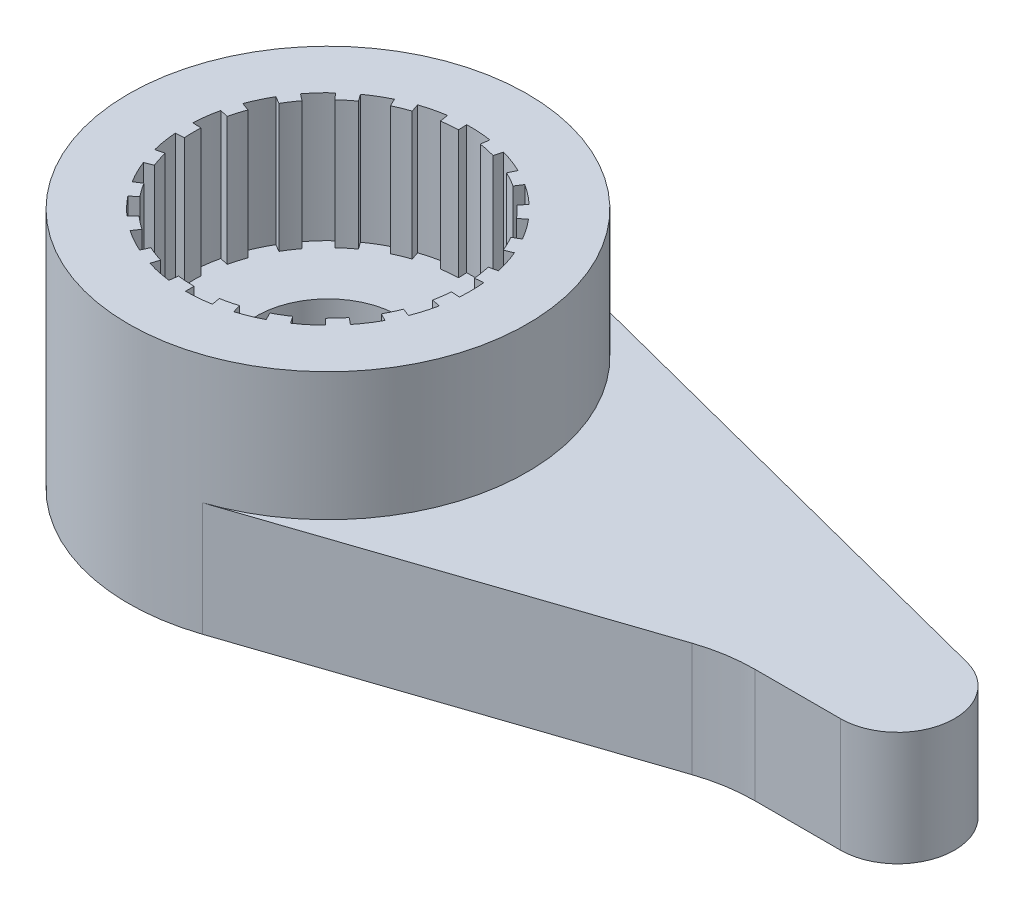
SolidWorks part; units mm, degrees
material "Nylon 6/10"
ref_plane "Front plane" through (0, 0, 0) normal (0, 0, 1) x (1, 0, 0)
ref_plane "Top plane" through (0, 0, 0) normal (0, 1, 0) x (1, 0, 0)
ref_plane "Right Plane" through (0, 0, 0) normal (1, 0, 0) x (0, 0, -1)
sketch "Sketch1" plane through (0, 0, 0) normal (0, 1, 0) x (1, 0, 0)
  circle A0 centre (0, 0) radius 2.5
  circle A1 centre (0, 0) radius 3.5
  dimension "D1" = 5
  dimension "D2" = 7
extrude "Boss-Extrude1" add sketch "Sketch1" along normal blind 2.25
sketch "Sketch6" plane through (0, 0, 0) normal (0, -1, 0) x (1, 0, 0)
  line L0 (0.4341, 2.462) -> (0.4081, 2.3143)
  line L1 (0.6927, 2.2456) -> (0.7369, 2.3889)
  line L2 (0, 2.35) -> (0, 0) construction
  line L3 (0, 0) -> (0.6927, 2.2456) construction
  line L4 (0, 0) -> (0.4081, 2.3143) construction
  line L5 (1.1405, 2.2247) -> (1.0721, 2.0912)
  line L6 (1.3238, 1.9417) -> (1.4083, 2.0656)
  line L7 (1.7456, 1.7897) -> (1.6409, 1.6823)
  line L8 (1.8373, 1.4652) -> (1.9546, 1.5587)
  line L9 (2.1956, 1.1956) -> (2.0638, 1.1239)
  line L10 (2.1876, 0.8586) -> (2.3272, 0.9134)
  line L11 (2.4504, 0.4954) -> (2.3034, 0.4656)
  line L12 (2.3434, 0.1756) -> (2.493, 0.1868)
  line L13 (2.4876, -0.2489) -> (2.3383, -0.234)
  line L14 (2.2911, -0.5229) -> (2.4373, -0.5563)
  line L15 (2.3037, -0.9711) -> (2.1655, -0.9128)
  line L16 (2.0352, -1.175) -> (2.1651, -1.25)
  line L17 (1.9151, -1.607) -> (1.8002, -1.5106)
  line L18 (1.5984, -1.7227) -> (1.7004, -1.8326)
  line L19 (1.3564, -2.1001) -> (1.275, -1.9741)
  line L20 (1.0196, -2.1173) -> (1.0847, -2.2524)
  line L21 (0.6771, -2.4066) -> (0.6365, -2.2622)
  line L22 (0.3502, -2.3238) -> (0.3726, -2.4721)
  line L23 (-0.0623, -2.4992) -> (-0.0586, -2.3493)
  line L24 (-0.3502, -2.3238) -> (-0.3726, -2.4721)
  line L25 (-0.7962, -2.3698) -> (-0.7484, -2.2276)
  line L26 (-1.0196, -2.1173) -> (-1.0847, -2.2524)
  line L27 (-1.4594, -2.0298) -> (-1.3718, -1.9081)
  line L28 (-1.5984, -1.7227) -> (-1.7004, -1.8326)
  line L29 (-1.9928, -1.5095) -> (-1.8733, -1.4189)
  line L30 (-2.0352, -1.175) -> (-2.1651, -1.25)
  line L31 (-2.3492, -0.8551) -> (-2.2083, -0.8037)
  line L32 (-2.2911, -0.5229) -> (-2.4373, -0.5563)
  line L33 (-2.4969, -0.1246) -> (-2.3471, -0.1171)
  line L34 (-2.3434, 0.1756) -> (-2.493, 0.1868)
  line L35 (-2.4227, 0.6169) -> (-2.2773, 0.5799)
  line L36 (-2.1876, 0.8586) -> (-2.3272, 0.9134)
  line L37 (-2.1332, 1.3036) -> (-2.0052, 1.2254)
  line L38 (-1.8373, 1.4652) -> (-1.9546, 1.5587)
  line L39 (-1.6542, 1.8745) -> (-1.555, 1.762)
  line L40 (-1.3238, 1.9417) -> (-1.4083, 2.0656)
  line L41 (-1.0282, 2.2788) -> (-0.9665, 2.142)
  line L42 (-0.6927, 2.2456) -> (-0.7369, 2.3889)
  line L43 (-0.3109, 2.4806) -> (-0.2922, 2.3318)
  line L44 (0, 2.35) -> (0, 2.5)
  arc A0 (0.6927, 2.2456) -> (0.4081, 2.3143) centre (0, 0) ccw
  circle A1 centre (0, 0) radius 2.5 construction
  arc A3 (0.7369, 2.3889) -> (0.4341, 2.462) centre (0, 0) ccw
  arc A4 (0.4081, 2.3143) -> (0, 2.35) centre (0, 0) ccw construction
  arc A5 (1.4083, 2.0656) -> (1.1405, 2.2247) centre (0, 0) ccw
  arc A6 (1.3238, 1.9417) -> (1.0721, 2.0912) centre (0, 0) ccw
  arc A7 (1.9546, 1.5587) -> (1.7456, 1.7897) centre (0, 0) ccw
  arc A8 (1.8373, 1.4652) -> (1.6409, 1.6823) centre (0, 0) ccw
  arc A9 (2.3272, 0.9134) -> (2.1956, 1.1956) centre (0, 0) ccw
  arc A10 (2.1876, 0.8586) -> (2.0638, 1.1239) centre (0, 0) ccw
  arc A11 (2.493, 0.1868) -> (2.4504, 0.4954) centre (0, 0) ccw
  arc A12 (2.3434, 0.1756) -> (2.3034, 0.4656) centre (0, 0) ccw
  arc A13 (2.4373, -0.5563) -> (2.4876, -0.2489) centre (0, 0) ccw
  arc A14 (2.2911, -0.5229) -> (2.3383, -0.234) centre (0, 0) ccw
  arc A15 (2.1651, -1.25) -> (2.3037, -0.9711) centre (0, 0) ccw
  arc A16 (2.0352, -1.175) -> (2.1655, -0.9128) centre (0, 0) ccw
  arc A17 (1.7004, -1.8326) -> (1.9151, -1.607) centre (0, 0) ccw
  arc A18 (1.5984, -1.7227) -> (1.8002, -1.5106) centre (0, 0) ccw
  arc A19 (1.0847, -2.2524) -> (1.3564, -2.1001) centre (0, 0) ccw
  arc A20 (1.0196, -2.1173) -> (1.275, -1.9741) centre (0, 0) ccw
  arc A21 (0.3726, -2.4721) -> (0.6771, -2.4066) centre (0, 0) ccw
  arc A22 (0.3502, -2.3238) -> (0.6365, -2.2622) centre (0, 0) ccw
  arc A23 (-0.3726, -2.4721) -> (-0.0623, -2.4992) centre (0, 0) ccw
  arc A24 (-0.3502, -2.3238) -> (-0.0586, -2.3493) centre (0, 0) ccw
  arc A25 (-1.0847, -2.2524) -> (-0.7962, -2.3698) centre (0, 0) ccw
  arc A26 (-1.0196, -2.1173) -> (-0.7484, -2.2276) centre (0, 0) ccw
  arc A27 (-1.7004, -1.8326) -> (-1.4594, -2.0298) centre (0, 0) ccw
  arc A28 (-1.5984, -1.7227) -> (-1.3718, -1.9081) centre (0, 0) ccw
  arc A29 (-2.1651, -1.25) -> (-1.9928, -1.5095) centre (0, 0) ccw
  arc A30 (-2.0352, -1.175) -> (-1.8733, -1.4189) centre (0, 0) ccw
  arc A31 (-2.4373, -0.5563) -> (-2.3492, -0.8551) centre (0, 0) ccw
  arc A32 (-2.2911, -0.5229) -> (-2.2083, -0.8037) centre (0, 0) ccw
  arc A33 (-2.493, 0.1868) -> (-2.4969, -0.1246) centre (0, 0) ccw
  arc A34 (-2.3434, 0.1756) -> (-2.3471, -0.1171) centre (0, 0) ccw
  arc A35 (-2.3272, 0.9134) -> (-2.4227, 0.6169) centre (0, 0) ccw
  arc A36 (-2.1876, 0.8586) -> (-2.2773, 0.5799) centre (0, 0) ccw
  arc A37 (-1.9546, 1.5587) -> (-2.1332, 1.3036) centre (0, 0) ccw
  arc A38 (-1.8373, 1.4652) -> (-2.0052, 1.2254) centre (0, 0) ccw
  arc A39 (-1.4083, 2.0656) -> (-1.6542, 1.8745) centre (0, 0) ccw
  arc A40 (-1.3238, 1.9417) -> (-1.555, 1.762) centre (0, 0) ccw
  arc A41 (-0.7369, 2.3889) -> (-1.0282, 2.2788) centre (0, 0) ccw
  arc A42 (-0.6927, 2.2456) -> (-0.9665, 2.142) centre (0, 0) ccw
  arc A43 (0, 2.5) -> (-0.3109, 2.4806) centre (0, 0) ccw
  arc A44 (0, 2.35) -> (-0.2922, 2.3318) centre (0, 0) ccw
  dimension "D1" = 0.15
  dimension "D2" = 17.143
  dimension "D3" = 10
  dimension "D4" = 21
extrude "Boss-Extrude4" add sketch "Sketch6" against normal up to surface (2.25 mm away) up to face at (0, 2.25, 3.5)
sketch "Sketch2" plane through (0, 0, 0) normal (0, 1, 0) x (1, 0, 0)
  line L0 (10.25, 0.9682) -> (0.875, 3.3889)
  line L2 (0, 0) -> (10, 0) construction
  line L6 (1.1153, -3.3176) -> (7.5441, -1.1564)
  line L7 (8.5, -1) -> (10, -1)
  circle A0 centre (0, 0) radius 3.5 construction
  arc A1 (1.1153, -3.3176) -> (0.875, 3.3889) centre (0, 0) ccw
  arc A2 (10, -1) -> (10.25, 0.9682) centre (10, 0) ccw
  arc A5 (7.5441, -1.1564) -> (8.5, -1) centre (8.5, -4) cw
  dimension "D1" = 10
  dimension "D2" = 1
  dimension "D3" = 3
  dimension "D4" = 1.5
extrude "Boss-Extrude2" add sketch "Sketch2" along normal blind 2 from offset 2.25 separate body
sketch "Sketch3" plane through (0, 2.25, 0) normal (0, 1, 0) x (1, 0, 0)
  circle A0 centre (0, 0) radius 1.25
  circle A3 centre (0, 0) radius 3.5
  circle A5 centre (0, 0) radius 3.5
  dimension "D2" = 2.5
  dimension "D1" = 0
extrude "Boss-Extrude3" add sketch "Sketch3" along normal up to vertex (2 mm away) up to point (0.875, 4.25, -3.3889)
sketch "Sketch4" plane through (0, 4.25, 0) normal (0, 1, 0) x (1, 0, 0)
  circle A0 centre (0, 0) radius 2.25
  dimension "D1" = 4.5
extrude "Cut-Extrude1" cut sketch "Sketch4" against normal blind 1.5
mirror "Mirror1" of bodies 105
delete or keep bodies "Body-Delete/Keep 1" type delete bodies bodies 105
